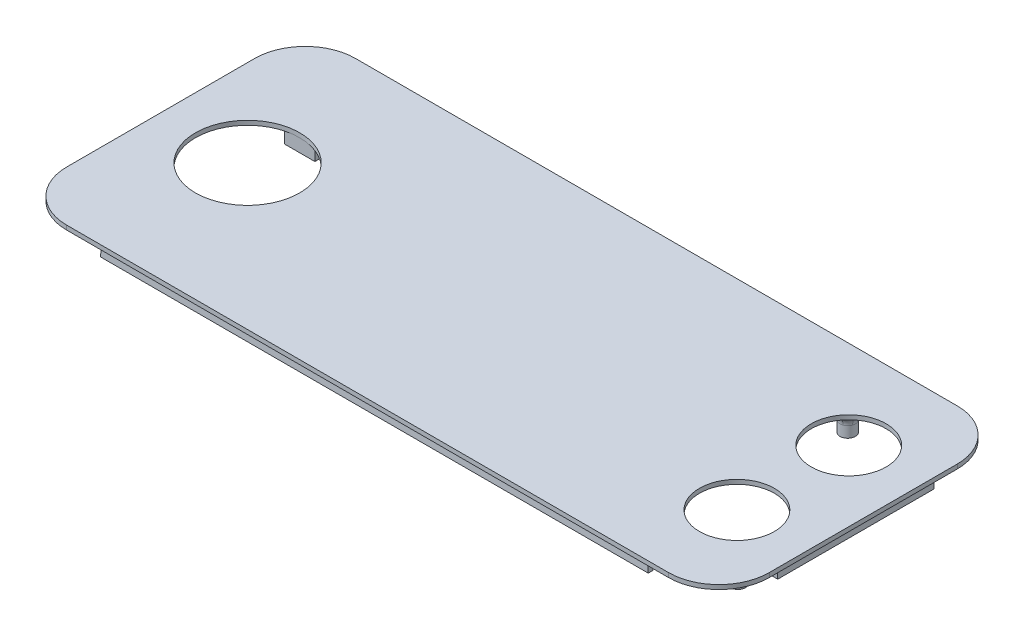
SolidWorks part; units mm, degrees
ref_plane "Front" through (0, 0, 0) normal (0, 0, 1) x (1, 0, 0)
ref_plane "Top" through (0, 0, 0) normal (0, 1, 0) x (1, 0, 0)
ref_plane "Right" through (0, 0, 0) normal (1, 0, 0) x (0, 0, -1)
sketch "Cover" plane through (0, 0, 0) normal (0, 1, 0) x (1, 0, 0)
  line L8 (85.9, -21.65) -> (85.9, 21.65)
  line L9 (74.3, 33.25) -> (-64.3, 33.25)
  line L10 (-75.9, 21.65) -> (-75.9, -21.65)
  line L11 (-64.3, -33.25) -> (74.3, -33.25)
  arc A8 (74.3, -33.25) -> (85.9, -21.65) centre (74.3, -21.65) ccw
  arc A9 (85.9, 21.65) -> (74.3, 33.25) centre (74.3, 21.65) ccw
  arc A10 (-64.3, 33.25) -> (-75.9, 21.65) centre (-64.3, 21.65) ccw
  arc A11 (-75.9, -21.65) -> (-64.3, -33.25) centre (-64.3, -21.65) ccw
sketch "Holes" plane through (0, 0, 0) normal (0, 1, 0) x (1, 0, 0)
  line L1 (69.675, 12.875) -> (78.3, 12.875) construction
  line L2 (85.9, -21.65) -> (85.9, 21.65) construction
  line L3 (69.675, 12.875) -> (69.675, 21.5) construction
  line L4 (74.3, 33.25) -> (-64.3, 33.25) construction
  line L5 (69.675, -12.875) -> (69.675, -21.5) construction
  line L6 (69.675, -12.875) -> (78.3, -12.875) construction
  line L7 (-64.3, -33.25) -> (74.3, -33.25) construction
  line L8 (-75.9, 21.65) -> (-75.9, -21.65) construction
  circle A0 centre (69.675, 12.875) radius 8.625
  circle A1 centre (69.675, -12.875) radius 8.625
  circle A2 centre (-55.9, 0) radius 12
  dimension "D1" = 17.25
  dimension "D2" = 17.25
  dimension "D7" = 24
  dimension "D3" = 7.6
  dimension "D4" = 11.75
  dimension "D5" = 7.6
  dimension "D6" = 11.75
  dimension "D8" = 20
  dimension "D9" = 33.25
  dimension "D10" = 25.75
  dimension "D11" = 43
extrude "Boss-Extrude1" add sketch "Cover" along normal blind 1
extrude "Cut-Extrude2" cut sketch "Holes" along normal blind 1
sketch "Sketch2" plane through (0, 0, 0) normal (0, -1, 0) x (-1, 0, 0)
  line L0 (67.9, 0) -> (43.9, 0) construction
  line L1 (55.9, -12) -> (55.9, 12) construction
  line L3 (59.4, -16.75) -> (52.4, -16.75)
  line L4 (59.4, -16.75) -> (59.4, -12)
  line L5 (59.4, -12) -> (52.4, -12)
  line L6 (52.4, -16.75) -> (52.4, -12)
  line L7 (59.4, -16.75) -> (52.4, -12) construction
  line L8 (59.4, -12) -> (52.4, -16.75) construction
  line L9 (59.4, 12) -> (52.4, 12)
  line L10 (59.4, 12) -> (59.4, 16.75)
  line L11 (59.4, 16.75) -> (52.4, 16.75)
  line L12 (52.4, 12) -> (52.4, 16.75)
  line L13 (59.4, 12) -> (52.4, 16.75) construction
  line L14 (59.4, 16.75) -> (52.4, 12) construction
  circle A2 centre (55.9, 0) radius 12 construction
  point P0 (55.9, -14.375)
  point P12 (55.9, 14.375)
  dimension "D1" = 7
  dimension "D2" = 7
  dimension "D3" = 0
  dimension "D4" = 0
  dimension "D5" = 4.75
  dimension "D6" = 4.75
extrude "Boss-Extrude2" add sketch "Sketch2" along normal blind 3
sketch "Sketch3" plane through (0, -3, 0) normal (0, -1, 0) x (-1, 0, 0)
  line L0 (55.9, -16.75) -> (55.9, -12) construction
  line L1 (52.4, -16.75) -> (59.4, -16.75) construction
  line L2 (59.4, -12) -> (52.4, -12) construction
  line L3 (55.9, -12) -> (59.4, -14.375) construction
  line L4 (59.4, -16.75) -> (59.4, -12) construction
  line L5 (59.4, -14.375) -> (52.4, -14.375) construction
  line L6 (52.4, -12) -> (52.4, -16.75) construction
  line L7 (55.9, 16.75) -> (55.9, 12) construction
  line L8 (59.4, 16.75) -> (52.4, 16.75) construction
  line L9 (52.4, 12) -> (59.4, 12) construction
  line L10 (52.4, 14.375) -> (59.4, 14.375) construction
  line L11 (52.4, 16.75) -> (52.4, 12) construction
  line L12 (59.4, 12) -> (59.4, 16.75) construction
  circle A0 centre (55.9, -14.375) radius 1
  circle A1 centre (55.9, 14.375) radius 1
  point P28 (55.9, -14.375)
  point P29 (55.9, 14.375)
  dimension "D1" = 2
  dimension "D2" = 2
extrude "Cut-Extrude3" cut sketch "Sketch3" against normal blind 2.5
sketch "Board Profile" plane through (0, 0, 0) normal (0, -1, 0) x (1, 0, 0)
  line L0 (74.3, -33.25) -> (-64.3, -33.25) construction
  line L1 (0.1098, -15.25) -> (0.1098, 2.75) construction
  line L2 (0.1098, -15.25) -> (43.1098, -15.25) construction
  line L3 (43.1098, -15.25) -> (43.1098, 2.75) construction
  line L4 (0.1098, 2.75) -> (43.1098, 2.75) construction
  line L5 (0.1098, -15.25) -> (43.1098, 2.75) construction
  line L6 (43.1098, -15.25) -> (0.1098, 2.75) construction
  point P0 (21.6098, -6.25)
  dimension "D1" = 18
  dimension "D2" = 43
  dimension "D3" = 18
  dimension "D4" = 43
  dimension "D5" = 18
sketch "Board Post Holes" plane through (0, 0, 0) normal (0, -1, 0) x (-1, 0, 0)
  line L0 (-0.1098, 15.25) -> (-0.1098, -2.75) construction
  line L1 (-0.1098, -2.75) -> (-43.1098, -2.75) construction
  line L2 (-0.1098, 15.25) -> (-43.1098, 15.25) construction
  line L3 (-43.1098, 15.25) -> (-43.1098, -2.75) construction
  circle A0 centre (-2.0098, -0.85) radius 1.75
  circle A1 centre (-2.0098, 13.35) radius 1.75
  circle A2 centre (-41.2098, 13.35) radius 1.75
  circle A3 centre (-41.2098, -0.85) radius 1.75
  circle A4 centre (-2.0098, 13.35) radius 1
  circle A5 centre (-2.0098, -0.85) radius 1
  circle A6 centre (-41.2098, -0.85) radius 1
  circle A7 centre (-41.2098, 13.35) radius 1
  dimension "D1" = 3.5
  dimension "D2" = 3.5
  dimension "D3" = 3.5
  dimension "D4" = 3.5
  dimension "D13" = 2
  dimension "D14" = 2
  dimension "D15" = 2
  dimension "D16" = 2
  dimension "D5" = 1.9
  dimension "D6" = 1.9
  dimension "D7" = 1.9
  dimension "D8" = 1.9
  dimension "D9" = 1.9
  dimension "D10" = 1.9
  dimension "D11" = 1.9
  dimension "D12" = 1.9
  dimension "D17" = 39.2
  dimension "D18" = 14.2
extrude "Boss-Extrude3" add sketch "Board Post Holes" along normal blind 5
sketch "End Stops" plane through (0, 0, 0) normal (0, -1, 0) x (1, 0, 0)
  line L0 (0, 0) -> (85.9, 0) construction
  line L1 (-74.2, 18.9625) -> (-72.4, 18.9625)
  line L2 (-74.2, 18.9625) -> (-74.2, -17.0375)
  line L3 (-74.2, -17.0375) -> (-72.4, -17.0375)
  line L4 (-72.4, 18.9625) -> (-72.4, -17.0375)
  line L5 (-74.2, 18.9625) -> (-72.4, -17.0375) construction
  line L6 (-74.2, -17.0375) -> (-72.4, 18.9625) construction
  line L7 (82.4, 18) -> (84.2, 18)
  line L8 (82.4, 18) -> (82.4, -18)
  line L9 (82.4, -18) -> (84.2, -18)
  line L10 (84.2, 18) -> (84.2, -18)
  line L11 (82.4, 18) -> (84.2, -18) construction
  line L12 (82.4, -18) -> (84.2, 18) construction
  line L13 (85.9, 21.65) -> (85.9, -21.65) construction
  line L14 (0, 0) -> (-75.9, 0) construction
  line L15 (-75.9, -21.65) -> (-75.9, 21.65) construction
  point P4 (-73.3, 0.9625)
  point P9 (83.3, 0)
  dimension "D1" = 1.8
  dimension "D2" = 1.8
  dimension "D3" = 36
  dimension "D4" = 36
  dimension "D5" = 1.7
  dimension "D6" = 1.7
extrude "Boss-Extrude4" add sketch "End Stops" along normal blind 3
sketch "Sketch7" plane through (0, 0, 0) normal (0, -1, 0) x (1, 0, 0)
  line L0 (74.3, -33.25) -> (-64.3, -33.25) construction
  line L1 (-57.9212, 31.55) -> (67.9212, 31.55)
  line L2 (-57.9212, 31.55) -> (-57.9212, 30.75)
  line L3 (-57.9212, 30.75) -> (67.9212, 30.75)
  line L4 (67.9212, 31.55) -> (67.9212, 30.75)
  line L5 (-57.9212, 31.55) -> (67.9212, 30.75) construction
  line L6 (-57.9212, 30.75) -> (67.9212, 31.55) construction
  line L7 (-58.5474, -30.75) -> (68.5474, -30.75)
  line L8 (-58.5474, -30.75) -> (-58.5474, -31.55)
  line L9 (-58.5474, -31.55) -> (68.5474, -31.55)
  line L10 (68.5474, -30.75) -> (68.5474, -31.55)
  line L11 (-58.5474, -30.75) -> (68.5474, -31.55) construction
  line L12 (-58.5474, -31.55) -> (68.5474, -30.75) construction
  line L13 (-64.3, 33.25) -> (74.3, 33.25) construction
  line L14 (-75.9, 0) -> (85.9, 0) construction
  line L15 (-75.9, -21.65) -> (-75.9, 21.65) construction
  line L16 (85.9, 21.65) -> (85.9, -21.65) construction
  line L17 (5, 33.25) -> (5, -33.25) construction
  point P4 (5, 31.15)
  point P9 (5, -31.15)
  dimension "D1" = 0.8
  dimension "D2" = 1.7
  dimension "D3" = 1.7
  dimension "D4" = 0.8
  dimension "D5" = 0
  dimension "D6" = 0
extrude "Boss-Extrude5" add sketch "Sketch7" along normal blind 3 draft 3 draft outward yes
fillet "Fillet1" radius 2 4 edges at (41.2098, 0, 2.6) (41.2098, 0, -11.6) (2.0098, 0, -11.6) (2.0098, 0, 2.6)
sketch "Sketch8" plane through (0, 0, 0) normal (0, -1, 0) x (1, 0, 0)
  line L0 (69.675, 12.875) -> (69.675, -12.875) construction
  line L1 (69.675, 0) -> (69.675, 21.5) construction
  line L2 (59.52, 22.8) -> (79.83, 22.8) construction
  line L3 (59.52, 22.8) -> (59.52, -22.8) construction
  line L4 (59.52, -22.8) -> (79.83, -22.8) construction
  line L5 (79.83, 22.8) -> (79.83, -22.8) construction
  line L6 (59.52, 22.8) -> (79.83, -22.8) construction
  line L7 (59.52, -22.8) -> (79.83, 22.8) construction
  line L8 (69.675, 0) -> (69.675, -21.5) construction
  line L10 (69.675, 0) -> (69.675, 22.8) construction
  line L11 (69.675, 0) -> (69.675, -22.8) construction
  line L12 (69.675, 0) -> (59.52, 0) construction
  line L13 (69.675, 0) -> (79.83, 0) construction
  circle A0 centre (60.92, 21.4) radius 1.75
  circle A1 centre (78.43, 21.4) radius 1.75
  circle A2 centre (60.92, -21.4) radius 1.75
  circle A3 centre (78.43, -21.4) radius 1.75
  point P2 (69.675, 0)
  dimension "D3" = 3.5
  dimension "D4" = 3.5
  dimension "D5" = 3.5
  dimension "D6" = 3.5
  dimension "D2" = 45.6
  dimension "D7" = 1.4
  dimension "D8" = 1.4
  dimension "D9" = 1.4
  dimension "D10" = 1.4
  dimension "D11" = 1.4
  dimension "D12" = 1.4
  dimension "D13" = 1.4
  dimension "D14" = 1.4
extrude "Boss-Extrude6" add sketch "Sketch8" along normal blind 5
sketch "Sketch9" plane through (0, -5, 0) normal (0, -1, 0) x (-1, 0, 0)
  circle A0 centre (-60.92, -21.4) radius 0.55
  circle A1 centre (-78.43, -21.4) radius 0.55
  circle A2 centre (-60.92, 21.4) radius 0.55
  circle A3 centre (-78.43, 21.4) radius 0.55
  dimension "D1" = 1.1
  dimension "D2" = 1.1
  dimension "D3" = 1.1
  dimension "D4" = 1.1
extrude "Cut-Extrude4" cut sketch "Sketch9" against normal blind 4
fillet "Fillet2" radius 2.5 4 edges at (78.43, 0, -19.65) (60.92, 0, -19.65) (78.43, 0, 23.15) (60.92, 0, 23.15)
